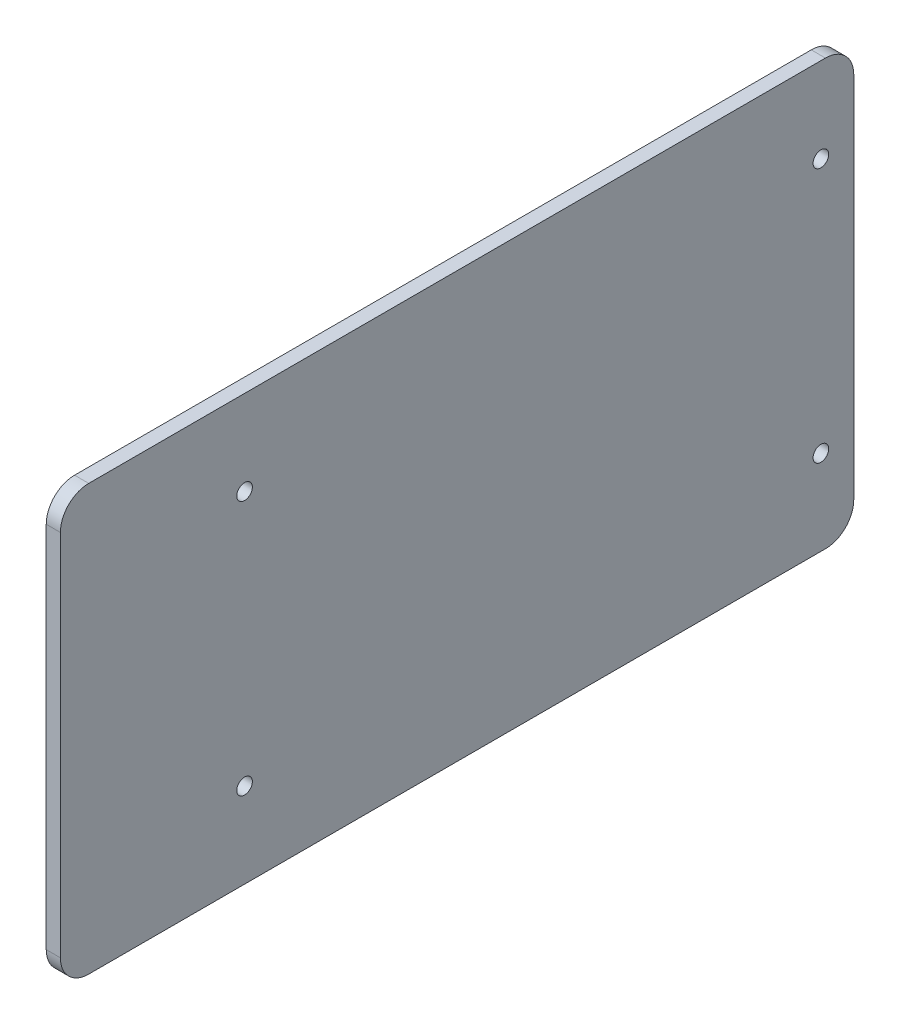
SolidWorks part; units mm, degrees
material "CoreCork NL25"
ref_plane "Płaszczyzna XY" through (0, 0, 0) normal (0, 0, 1) x (1, 0, 0)
ref_plane "Płaszczyzna XZ" through (0, 0, 0) normal (0, 1, 0) x (1, 0, 0)
ref_plane "Płaszczyzna YZ" through (0, 0, 0) normal (1, 0, 0) x (0, 0, -1)
ref_plane "Płaszczyzna1" through (1037.6, 0, 0) normal (1, 0, 0) x (0, 0, -1)
sketch "Szkic1" plane through (1037.6, 0, 0) normal (1, 0, 0) x (0, 0, -1)
  line L1 (-892.51, 75) -> (-632.51, 75)
  line L2 (-902.51, 65) -> (-902.51, -65)
  line L3 (-892.51, -75) -> (-632.51, -75)
  line L4 (-622.51, 65) -> (-622.51, -65)
  line L5 (-902.51, 75) -> (-622.51, -75) construction
  line L6 (-902.51, -75) -> (-622.51, 75) construction
  arc A0 (-632.51, 75) -> (-622.51, 65) centre (-632.51, 65) cw
  arc A1 (-622.51, -65) -> (-632.51, -75) centre (-632.51, -65) cw
  arc A2 (-892.51, -75) -> (-902.51, -65) centre (-892.51, -65) cw
  arc A3 (-902.51, 65) -> (-892.51, 75) centre (-892.51, 65) cw
  point P0 (-762.51, 0)
  dimension "D4" = 10
  dimension "D1" = 150
  dimension "D2" = 280
  dimension "D3" = 762.51
extrude "Dodanie-wyciągnięcie1" add sketch "Szkic1" against normal blind 5
sketch "Szkic2" plane through (1032.6, 0, 0) normal (-1, 0, 0) x (0, 0, 1)
  line L0 (622.51, 53.7228) -> (634.12, 53.7228)
  line L1 (622.51, -65) -> (622.51, 65) construction
  line L2 (634.12, 75) -> (634.12, 45)
  line L3 (632.51, 75) -> (892.51, 75) construction
  line L4 (634.12, -75) -> (634.12, -45)
  line L5 (892.51, -75) -> (632.51, -75) construction
hole_wizard "Otwór pod śrubę M51" positions "Szkic3" profile "Szkic4" hole size "M5" standard "ISO"
sketch "Szkic3" plane through (1032.6, 0, 0) normal (-1, 0, 0) x (0, 0, 1)
  point P0 (634.12, 45)
  point P3 (634.12, -45)
sketch "Szkic4" plane through (1032.6, 45, 634.12) normal (0, 1, 0) x (0, 0, 1)
  line L0 (0, 0) -> (0, 15.6524)
  line L1 (0, 15.6524) -> (2.75, 14)
  line L2 (2.75, 14) -> (2.75, 0)
  line L5 (2.75, 0) -> (0, 0)
  line L10 (0, 15.6524) -> (-2.75, 14) construction
  line L11 (0, -6.35) -> (0, 107.95) construction
  dimension "Średnica otworu" = 5.5
  dimension "Głębokość otworu" = 14
  dimension "Kąt wiertła" = 118
sketch "Szkic5" plane through (1032.6, 0, 0) normal (-1, 0, 0) x (0, 0, 1)
  line L0 (634.12, 45) -> (837.51, 45)
  line L1 (634.12, -45) -> (837.51, -45)
hole_wizard "Otwór pod śrubę M52" positions "Szkic6" profile "Szkic7" hole size "M5" standard "ISO"
sketch "Szkic6" plane through (1032.6, 0, 0) normal (-1, 0, 0) x (0, 0, 1)
  point P0 (837.51, 45)
  point P3 (837.51, -45)
sketch "Szkic7" plane through (1032.6, 45, 837.51) normal (0, 1, 0) x (0, 0, 1)
  line L0 (0, 0) -> (0, 15.6524)
  line L1 (0, 15.6524) -> (2.75, 14)
  line L2 (2.75, 14) -> (2.75, 0)
  line L5 (2.75, 0) -> (0, 0)
  line L10 (0, 15.6524) -> (-2.75, 14) construction
  line L11 (0, -6.35) -> (0, 107.95) construction
  dimension "Średnica otworu" = 5.5
  dimension "Głębokość otworu" = 14
  dimension "Kąt wiertła" = 118
